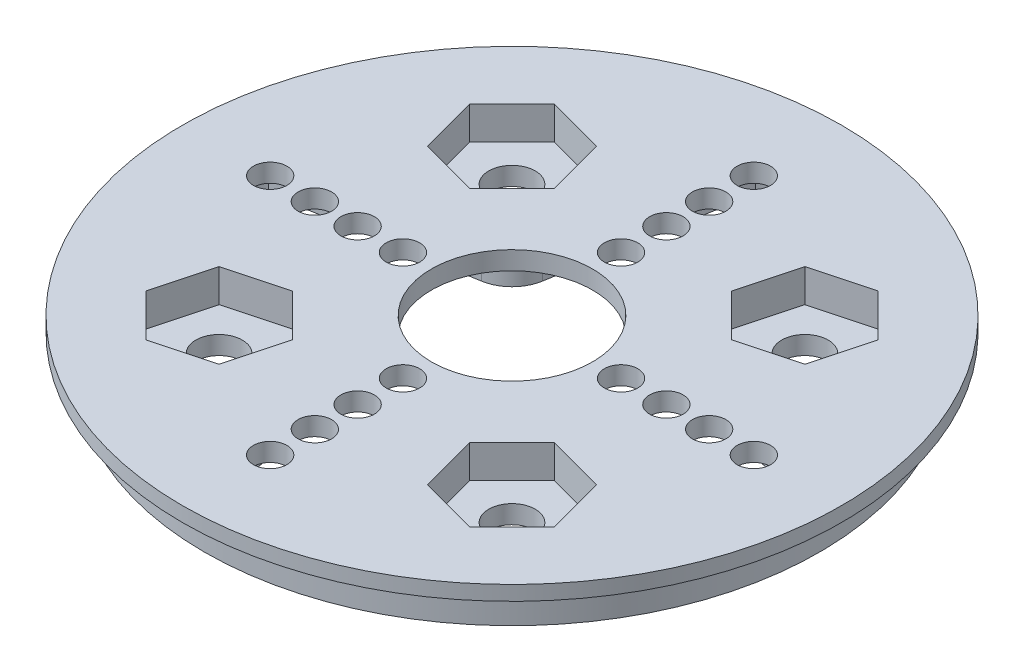
SolidWorks part; units mm, degrees
ref_plane "Front Plane" through (0, 0, 0) normal (0, 0, 1) x (1, 0, 0)
ref_plane "Top Plane" through (0, 0, 0) normal (0, 1, 0) x (1, 0, 0)
ref_plane "Right Plane" through (0, 0, 0) normal (1, 0, 0) x (0, 0, -1)
sketch "Sketch2" plane through (0, 0, 0) normal (0, 1, 0) x (1, 0, 0)
  circle A0 centre (0, 0) radius 21
extrude "Boss-Extrude1" add sketch "Sketch2" along normal blind 3.5
sketch "Sketch1" plane through (0, 0, 0) normal (0, 1, 0) x (1, 0, 0)
  line L0 (-19.41, 0) -> (20, 0) construction
  line L1 (0, 20) -> (0, -20) construction
  line L2 (-2.3825, -18.9992) -> (-4.4832, -6.5648)
  line L3 (2.3825, -18.9992) -> (4.4832, -6.5648)
  line L4 (-18.9992, 2.3825) -> (-6.5648, 4.4832)
  line L5 (-18.9992, -2.3825) -> (-6.5648, -4.4832)
  line L6 (18.9992, -2.3825) -> (6.5648, -4.4832)
  line L7 (18.9992, 2.3825) -> (6.5648, 4.4832)
  line L8 (2.3825, 18.9992) -> (4.4832, 6.5648)
  line L9 (-2.3825, 18.9992) -> (-4.4832, 6.5648)
  circle A0 centre (0, 0) radius 20 construction
  circle A1 centre (0, 0) radius 3.6 construction
  arc A2 (18.9992, -2.3825) -> (18.9992, 2.3825) centre (16.6638, 0) ccw
  arc A3 (-2.3825, -18.9992) -> (2.3825, -18.9992) centre (0, -16.6638) ccw
  arc A4 (-18.9992, 2.3825) -> (-18.9992, -2.3825) centre (-16.6638, 0) ccw
  arc A5 (2.3825, 18.9992) -> (-2.3825, 18.9992) centre (0, 16.6638) ccw
  arc A6 (4.4832, -6.5648) -> (6.5648, -4.4832) centre (6.988, -6.988) cw
  arc A7 (6.5648, 4.4832) -> (4.4832, 6.5648) centre (6.988, 6.988) cw
  arc A8 (-4.4832, 6.5648) -> (-6.5648, 4.4832) centre (-6.988, 6.988) cw
  arc A9 (-6.5648, -4.4832) -> (-4.4832, -6.5648) centre (-6.988, -6.988) cw
  point P27 (0, 0)
  point P52 (0, 0)
  dimension "D1" = 4
extrude "Cut-Extrude1" cut sketch "Sketch1" along normal blind 2.25
sketch "Sketch4" plane through (0, 3.5, 0) normal (0, 1, 0) x (1, 0, 0)
  line L0 (0, 21) -> (0, -21) construction
  line L1 (-21, 0) -> (21, 0) construction
  circle A0 centre (0, 0) radius 21 construction
  circle A1 centre (0, 0) radius 5.5
  circle A2 centre (7.445, 0) radius 1.143
  circle A3 centre (10.54, 0) radius 1.143
  circle A4 centre (13.46, 0) radius 1.143
  circle A5 centre (16.51, 0) radius 1.143
  circle A6 centre (10, 10) radius 1.5875
  circle A7 centre (0, -7.445) radius 1.143
  circle A8 centre (0, -10.54) radius 1.143
  circle A9 centre (0, -13.46) radius 1.143
  circle A10 centre (0, -16.51) radius 1.143
  circle A11 centre (10, -10) radius 1.5875
  circle A12 centre (-7.445, 0) radius 1.143
  circle A13 centre (-10.54, 0) radius 1.143
  circle A14 centre (-13.46, 0) radius 1.143
  circle A15 centre (-16.51, 0) radius 1.143
  circle A16 centre (-10, -10) radius 1.5875
  circle A17 centre (0, 7.445) radius 1.143
  circle A18 centre (0, 10.54) radius 1.143
  circle A19 centre (0, 13.46) radius 1.143
  circle A20 centre (0, 16.51) radius 1.143
  circle A21 centre (-10, 10) radius 1.5875
  point P52 (0, 0)
  dimension "D1" = 4
extrude "Cut-Extrude2" cut sketch "Sketch4" against normal through all
sketch "Sketch5" plane through (0, 3.5, 0) normal (0, 1, 0) x (1, 0, 0)
  line L0 (0, 0) -> (10, 10) construction
  line L2 (11.056, -13.941) -> (13.941, -11.056)
  line L3 (13.941, -11.056) -> (12.885, -7.115)
  line L4 (12.885, -7.115) -> (8.944, -6.059)
  line L5 (8.944, -6.059) -> (6.059, -8.944)
  line L6 (6.059, -8.944) -> (7.115, -12.885)
  line L7 (-8.944, 6.059) -> (-6.059, 8.944)
  line L8 (-6.059, 8.944) -> (-7.115, 12.885)
  line L9 (-7.115, 12.885) -> (-11.056, 13.941)
  line L10 (-11.056, 13.941) -> (-13.941, 11.056)
  line L11 (-13.941, 11.056) -> (-12.885, 7.115)
  line L12 (-12.885, 7.115) -> (-8.944, 6.059)
  line L13 (12.885, 7.115) -> (13.941, 11.056)
  line L14 (13.941, 11.056) -> (11.056, 13.941)
  line L15 (11.056, 13.941) -> (7.115, 12.885)
  line L16 (7.115, 12.885) -> (6.059, 8.944)
  line L17 (6.059, 8.944) -> (8.944, 6.059)
  line L18 (8.944, 6.059) -> (12.885, 7.115)
  line L19 (-7.115, -12.885) -> (-6.059, -8.944)
  line L20 (-6.059, -8.944) -> (-8.944, -6.059)
  line L21 (-8.944, -6.059) -> (-12.885, -7.115)
  line L22 (-12.885, -7.115) -> (-13.941, -11.056)
  line L23 (-13.941, -11.056) -> (-11.056, -13.941)
  line L24 (-11.056, -13.941) -> (-7.115, -12.885)
  line L25 (-10, 10) -> (0, 0) construction
  line L26 (7.115, -12.885) -> (11.056, -13.941)
  circle A0 centre (10, -10) radius 3.5334 construction
  circle A1 centre (-10, 10) radius 3.5334 construction
  circle A2 centre (10, 10) radius 3.5334 construction
  circle A3 centre (-10, -10) radius 3.5334 construction
extrude "Cut-Extrude4" cut sketch "Sketch5" against normal blind 2.25
sketch "Sketch6" plane through (0, 0, 0) normal (0, 0, 1) x (1, 0, 0)
  line L0 (21, 3.5) -> (-21, 3.5) construction
  line L1 (-20.3515, 3.5) -> (-22.5, 3.5)
  line L2 (-20.3515, 3.5) -> (-20.3515, 2.5)
  line L3 (-20.3515, 2.5) -> (-22.5, 2.5)
  line L4 (-22.5, 3.5) -> (-22.5, 2.5)
  line L5 (-21, 3.5) -> (-21, 0) construction
  line L6 (0, 0) -> (0, 5.1601) construction
  dimension "D1" = 1
  dimension "D2" = 1.5
revolve "Revolve1" add sketch "Sketch6" angle 360 about L6
